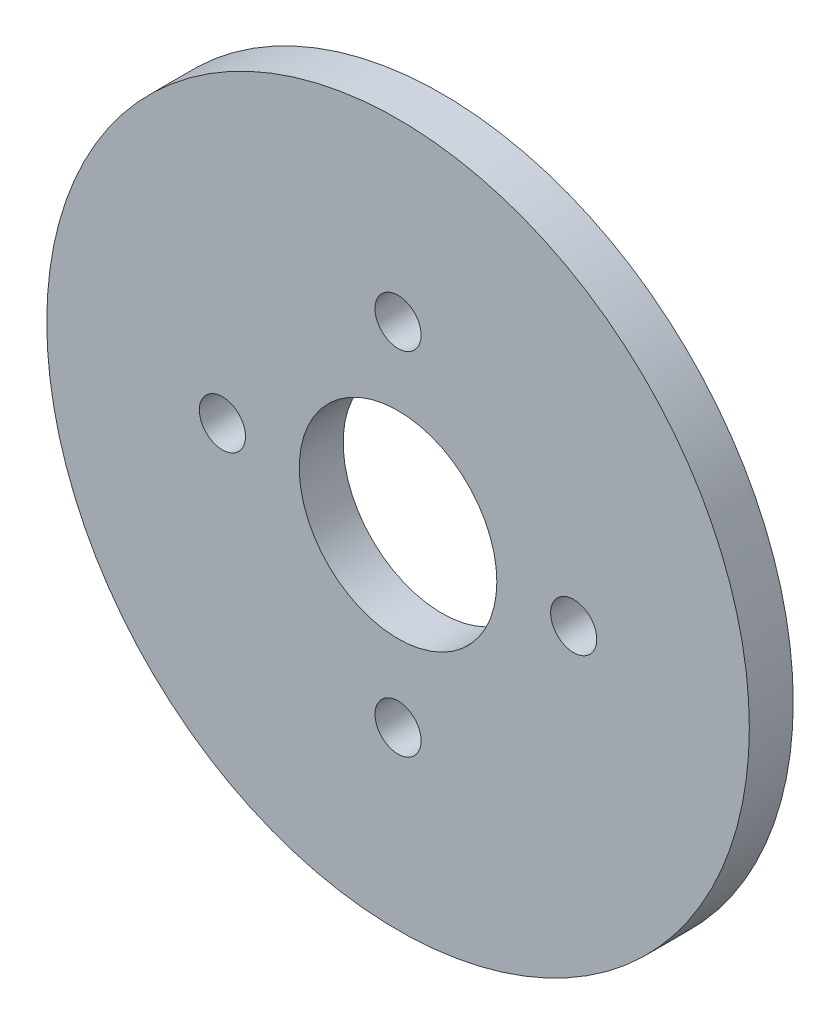
SolidWorks part; units mm, degrees
ref_plane "Front Plane" through (0, 0, 0) normal (0, 0, 1) x (1, 0, 0)
ref_plane "Top Plane" through (0, 0, 0) normal (0, 1, 0) x (1, 0, 0)
ref_plane "Right Plane" through (0, 0, 0) normal (1, 0, 0) x (0, 0, -1)
sketch "Sketch1" plane through (0, 0, 0) normal (0, 0, 1) x (1, 0, 0)
  circle A0 centre (0, 0) radius 4.5
  circle A1 centre (0, 0) radius 16
  circle A2 centre (0, 0) radius 8 construction
  circle A3 centre (0, 8) radius 1.05
  circle A4 centre (8, 0) radius 1.05
  circle A5 centre (0, -8) radius 1.05
  circle A6 centre (-8, 0) radius 1.05
  point P16 (0, 0)
  dimension "D1" = 32
  dimension "D2" = 9
  dimension "D3" = 16
  dimension "D4" = 2.1
  dimension "D5" = 4
extrude "Boss-Extrude1" add sketch "Sketch1" along normal blind 2
